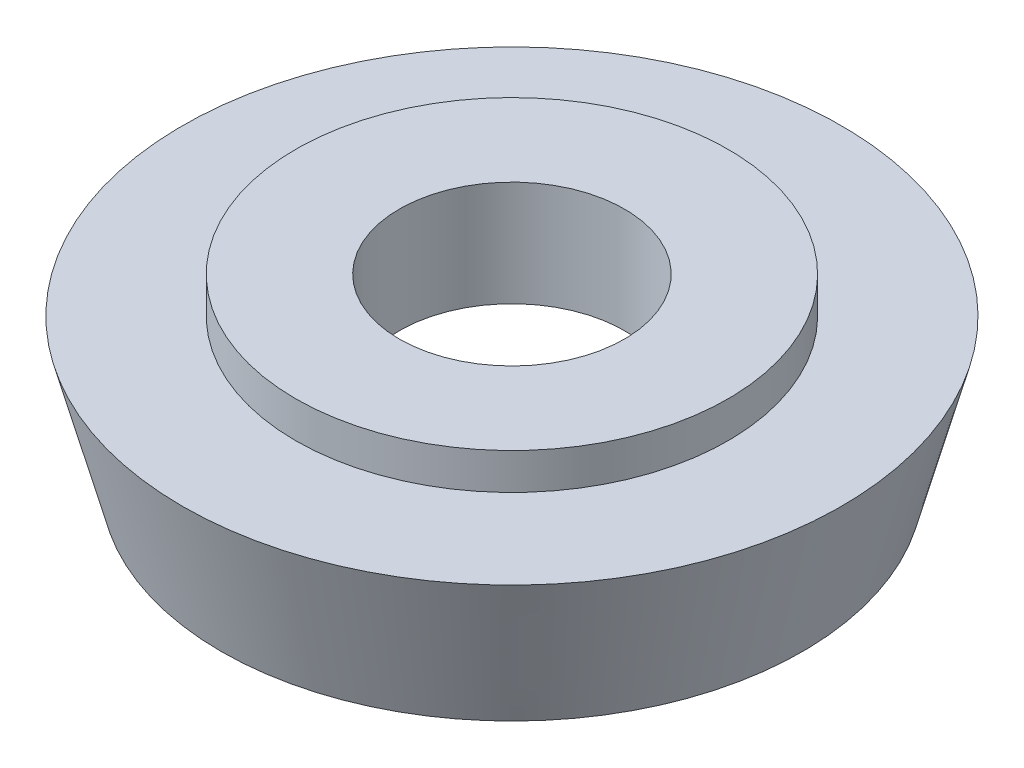
SolidWorks part; units mm, degrees
material "Delrin 2700 NC010, Low Viscosity Acetal Copolymer (SS)"
ref_plane "Front Plane" through (0, 0, 0) normal (0, 0, 1) x (1, 0, 0)
ref_plane "Top Plane" through (0, 0, 0) normal (0, 1, 0) x (1, 0, 0)
ref_plane "Right Plane" through (0, 0, 0) normal (1, 0, 0) x (0, 0, -1)
sketch "Sketch1" plane through (0, 0, 0) normal (0, 0, 1) x (1, 0, 0)
  line L0 (-1.55, 2.5) -> (-2.975, 2.5)
  line L1 (-2.975, 2.5) -> (-2.975, 2)
  line L2 (-2.975, 2) -> (-4.5359, 2)
  line L3 (-4.5359, 2) -> (-4, 0)
  line L4 (-4, 0) -> (-3.05, 0)
  line L5 (-3.05, 0) -> (-3.05, 1.05)
  line L6 (-3.05, 1.05) -> (-1.55, 1.05)
  line L7 (-1.55, 1.05) -> (-1.55, 2.5)
  line L8 (0, 2.5) -> (0, 0) construction
  point P11 (-1.9466, 1.9862)
  point P12 (-1.9269, 0)
  point P13 (-4.4565, 2.2233)
  point P14 (-3.8043, 0)
  point P15 (-1.55, 0.556)
  point P16 (-5.0052, 2)
  dimension "D1" = 2.5
  dimension "D2" = 3.1
  dimension "D3" = 6.1
  dimension "D4" = 5.95
  dimension "D5" = 15
  dimension "D6" = 2
  dimension "D7" = 1.05
  dimension "D8" = 8
revolve "Revolve1" add sketch "Sketch1" angle 360 about L8
